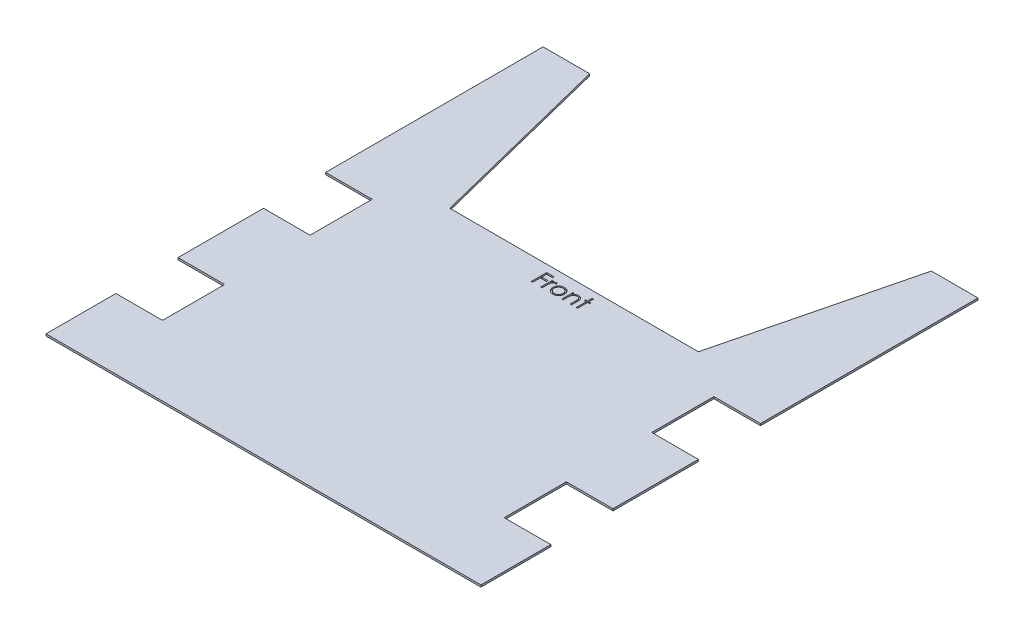
SolidWorks part; units mm, degrees
material "6061 Alloy"
ref_plane "Front Plane" through (0, 0, 0) normal (0, 0, 1) x (1, 0, 0)
ref_plane "Top Plane" through (0, 0, 0) normal (0, 1, 0) x (1, 0, 0)
ref_plane "Right Plane" through (0, 0, 0) normal (1, 0, 0) x (0, 0, -1)
sketch "Sketch1" plane through (0, 0, 0) normal (0, 1, 0) x (1, 0, 0)
  line L0 (-355.6, 254) -> (355.6, -254) construction
  line L1 (-279.4, 152.4) -> (-82.55, 152.4) construction
  line L2 (-355.6, 203.2) -> (-279.4, 203.2)
  line L3 (355.6, 190.5) -> (82.55, 190.5) construction
  line L4 (355.6, 203.2) -> (355.6, 101.6) construction
  line L5 (355.6, 114.3) -> (82.55, 114.3) construction
  line L6 (82.55, 190.5) -> (82.55, 114.3) construction
  line L7 (355.6, -50.8) -> (82.55, -50.8) construction
  line L8 (355.6, -38.1) -> (355.6, -139.7) construction
  line L9 (355.6, -127) -> (82.55, -127) construction
  line L10 (82.55, -50.8) -> (82.55, -127) construction
  line L11 (-355.6, -50.8) -> (-82.55, -50.8) construction
  line L12 (-355.6, -38.1) -> (-355.6, -139.7) construction
  line L13 (-355.6, -127) -> (-82.55, -127) construction
  line L14 (-82.55, -50.8) -> (-82.55, -127) construction
  line L15 (-355.6, 190.5) -> (-82.55, 190.5) construction
  line L16 (-355.6, 203.2) -> (-355.6, 101.6) construction
  line L17 (-355.6, 114.3) -> (-82.55, 114.3) construction
  line L18 (-203.2, 254) -> (203.2, 254)
  line L19 (-355.6, 254) -> (-355.6, 203.2)
  line L20 (-355.6, -254) -> (355.6, -254)
  line L21 (355.6, 254) -> (355.6, 203.2)
  line L22 (-82.55, 190.5) -> (-82.55, 114.3) construction
  line L23 (355.6, 101.6) -> (355.6, -38.1)
  line L24 (-355.6, 101.6) -> (-279.4, 101.6)
  line L25 (-279.4, 203.2) -> (-279.4, 101.6)
  line L26 (-355.6, -38.1) -> (-279.4, -38.1)
  line L27 (355.6, -139.7) -> (355.6, -254)
  line L28 (-355.6, -139.7) -> (-279.4, -139.7)
  line L29 (-279.4, -38.1) -> (-279.4, -139.7)
  line L30 (279.4, -38.1) -> (355.6, -38.1)
  line L31 (279.4, -38.1) -> (279.4, -139.7)
  line L32 (279.4, -139.7) -> (355.6, -139.7)
  line L33 (-355.6, 254) -> (355.6, 254) construction
  line L34 (355.6, 101.6) -> (279.4, 101.6)
  line L35 (-279.4, -88.9) -> (-82.55, -88.9) construction
  line L36 (355.6, 203.2) -> (279.4, 203.2)
  line L37 (279.4, 101.6) -> (279.4, 203.2)
  line L38 (-355.6, 101.6) -> (-355.6, -38.1)
  line L39 (-355.6, -139.7) -> (-355.6, -254)
  line L40 (-203.2, 254) -> (-279.4, 558.8)
  line L41 (-355.6, 254) -> (-355.6, 558.8)
  line L42 (-355.6, 558.8) -> (-279.4, 558.8)
  line L43 (-203.2, 254) -> (-203.2, 558.8) construction
  line L44 (203.2, 254) -> (279.4, 558.8)
  line L45 (355.6, 254) -> (355.6, 558.8)
  line L46 (355.6, 558.8) -> (279.4, 558.8)
  line L47 (-203.2, 558.8) -> (-279.4, 558.8) construction
  line L48 (279.4, 558.8) -> (203.2, 558.8) construction
  line L49 (203.2, 558.8) -> (203.2, 254) construction
  point P49 (0, 0)
  point P50 (0, 0)
  point P51 (0, 0)
  dimension "D1" = 273.05
  dimension "D2" = 76.2
  dimension "D3" = 101.6
  dimension "D4" = 127
  dimension "D5" = 101.6
  dimension "D6" = 711.2
  dimension "D7" = 508
  dimension "D8" = 76.2
  dimension "D9" = 76.2
  dimension "D10" = 304.8
  dimension "D11" = 152.4
extrude "Boss-Extrude1" add sketch "Sketch1" along normal blind 3.175
sketch "Sketch2" plane through (0, 3.175, 0) normal (0, 1, 0) x (1, 0, 0)
  line L0 (-355.6, 558.8) -> (-355.6, 203.2) construction
  line L1 (-355.6, 190.5) -> (-82.55, 190.5) construction
  line L2 (-355.6, 190.5) -> (-355.6, 114.3) construction
  line L3 (-355.6, 114.3) -> (-82.55, 114.3) construction
  line L4 (-82.55, 190.5) -> (-82.55, 114.3) construction
  line L5 (355.6, 203.2) -> (355.6, 558.8) construction
  line L6 (-355.6, -50.8) -> (-82.55, -50.8) construction
  line L7 (-355.6, -50.8) -> (-355.6, -127) construction
  line L8 (-355.6, -127) -> (-82.55, -127) construction
  line L9 (-82.55, -50.8) -> (-82.55, -127) construction
  line L10 (355.6, -127) -> (82.55, -127) construction
  line L11 (355.6, -127) -> (355.6, -50.8) construction
  line L12 (355.6, -50.8) -> (82.55, -50.8) construction
  line L13 (82.55, -127) -> (82.55, -50.8) construction
  line L15 (355.6, 114.3) -> (82.55, 114.3) construction
  line L16 (355.6, 114.3) -> (355.6, 190.5) construction
  line L17 (355.6, 190.5) -> (82.55, 190.5) construction
  line L18 (82.55, 114.3) -> (82.55, 190.5) construction
  line L19 (-355.6, -254) -> (355.6, -254) construction
  line L20 (-355.6, 152.4) -> (-82.55, 152.4) construction
  line L21 (203.2, 254) -> (-203.2, 254) construction
  dimension "D1" = 273.05
  dimension "D2" = 76.2
  dimension "D3" = 101.6
  dimension "D4" = 127
sketch "Sketch3" plane through (0, 3.175, 0) normal (0, 1, 0) x (1, 0, 0)
  text T0 "Front" font "Century Gothic" height 25.4
extrude "Cut-Extrude1" cut sketch "Sketch3" against normal blind 2.54
